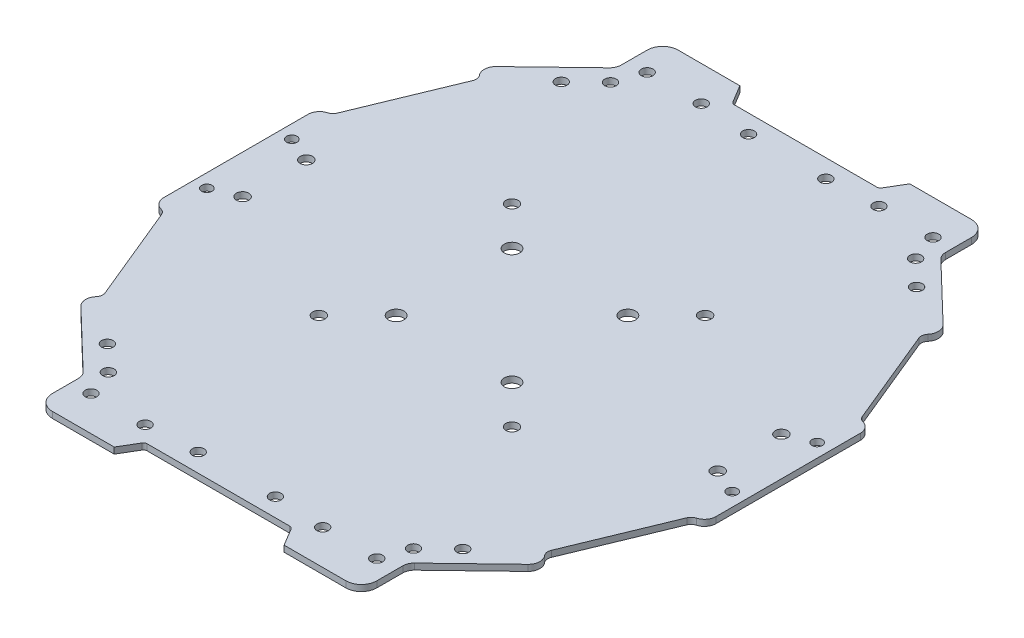
SolidWorks part; units mm, degrees
ref_plane "Front Plane" through (0, 0, 0) normal (0, 0, 1) x (1, 0, 0)
ref_plane "Top Plane" through (0, 0, 0) normal (0, 1, 0) x (1, 0, 0)
ref_plane "Right Plane" through (0, 0, 0) normal (1, 0, 0) x (0, 0, -1)
ref_plane "Plane1"
sketch "Sketch1" plane through (0, 0, 0) normal (0, 1, 0) x (-1, 0, 0)
  line L0 (59.7752, 259.0599) -> (56.7752, 264.0599)
  line L1 (56.7752, 264.0599) -> (36.7752, 264.0599)
  line L2 (36.7752, 264.0599) -> (36.7752, 252.0599)
  line L3 (36.7752, 252.0599) -> (18.7553, 234.7311)
  line L4 (18.7553, 234.7311) -> (21.5279, 231.8479)
  line L5 (21.5279, 231.8479) -> (10.2752, 204.5599)
  line L6 (10.2752, 204.5599) -> (7.2752, 204.5599)
  line L7 (7.2752, 204.5599) -> (7.2752, 183.0599)
  line L8 (7.2752, 183.0599) -> (7.2752, 161.5599)
  line L9 (7.2752, 161.5599) -> (10.2752, 161.5599)
  line L10 (10.2752, 161.5599) -> (21.5279, 134.2718)
  line L11 (21.5279, 134.2718) -> (18.7553, 131.3886)
  line L12 (18.7553, 131.3886) -> (36.7752, 114.0599)
  line L13 (36.7752, 114.0599) -> (36.7752, 102.0599)
  line L14 (36.7752, 102.0599) -> (56.7752, 102.0599)
  line L15 (56.7752, 102.0599) -> (59.7752, 107.0599)
  line L16 (59.7752, 107.0599) -> (78.7752, 107.0599)
  line L17 (78.7752, 107.0599) -> (97.7752, 107.0599)
  line L18 (97.7752, 107.0599) -> (100.7752, 102.0599)
  line L19 (100.7752, 102.0599) -> (120.7752, 102.0599)
  line L20 (120.7752, 102.0599) -> (120.7752, 114.0599)
  line L21 (120.7752, 114.0599) -> (138.795, 131.3886)
  line L22 (138.795, 131.3886) -> (136.0224, 134.2718)
  line L23 (136.0224, 134.2718) -> (147.2752, 161.5599)
  line L24 (147.2752, 161.5599) -> (150.2752, 161.5599)
  line L25 (150.2752, 161.5599) -> (150.2752, 183.0599)
  line L26 (150.2752, 183.0599) -> (150.2752, 204.5599)
  line L27 (150.2752, 204.5599) -> (147.2752, 204.5599)
  line L28 (147.2752, 204.5599) -> (136.0224, 231.8479)
  line L29 (136.0224, 231.8479) -> (138.795, 234.7311)
  line L30 (138.795, 234.7311) -> (120.7752, 252.0599)
  line L31 (120.7752, 252.0599) -> (120.7752, 264.0599)
  line L32 (120.7752, 264.0599) -> (100.7752, 264.0599)
  line L33 (100.7752, 264.0599) -> (97.7752, 259.0599)
  line L34 (97.7752, 259.0599) -> (78.7752, 259.0599)
  line L35 (78.7752, 259.0599) -> (59.7752, 259.0599)
  line L38 (78.7752, 259.0599) -> (78.7752, 107.0599) construction
  line L39 (150.2752, 183.0599) -> (7.2752, 183.0599) construction
  line L85 (91.8838, 199.6325) -> (91.9874, 199.5289)
  line L87 (95.3777, 196.1387) -> (95.4193, 196.097)
  circle A0 centre (55.7752, 111.0599) radius 1.5
  circle A1 centre (39.2752, 118.0599) radius 1.5
  circle A2 centre (53.7752, 208.0599) radius 1.6
  circle A3 centre (53.7752, 158.0599) radius 1.6
  circle A4 centre (17.2752, 174.8099) radius 1.6
  circle A5 centre (103.7752, 158.0599) radius 1.6
  circle A6 centre (93.7752, 198.0599) radius 2
  circle A7 centre (63.7752, 198.0599) radius 2
  circle A8 centre (63.7752, 168.0599) radius 2
  circle A9 centre (93.7752, 168.0599) radius 2
  circle A22 centre (41.7752, 255.0599) radius 1.5
  circle A23 centre (39.2752, 248.0599) radius 1.5
  circle A24 centre (10.7752, 194.0599) radius 1.35
  circle A25 centre (88.7752, 111.8099) radius 1.5
  circle A27 centre (115.7752, 111.0599) radius 1.5
  circle A28 centre (118.2752, 118.0599) radius 1.5
  circle A29 centre (140.2752, 174.8099) radius 1.6
  circle A30 centre (115.7752, 255.0599) radius 1.5
  circle A31 centre (88.7752, 254.3099) radius 1.5
  circle A32 centre (140.2752, 191.3099) radius 1.6
  circle A33 centre (146.7752, 194.0599) radius 1.35
  circle A53 centre (101.7752, 255.0599) radius 1.5
  circle A54 centre (118.2752, 248.0599) radius 1.5
  circle A55 centre (146.7752, 172.0599) radius 1.35
  circle A57 centre (101.7752, 111.0599) radius 1.5
  circle A69 centre (17.2752, 191.3099) radius 1.6
  circle A71 centre (55.7752, 255.0599) radius 1.5
  circle A73 centre (68.7752, 254.3099) radius 1.5
  circle A74 centre (10.7752, 172.0599) radius 1.35
  circle A76 centre (68.7752, 111.8099) radius 1.5
  circle A77 centre (41.7752, 111.0599) radius 1.5
  circle A82 centre (32.7752, 124.3099) radius 1.5
  circle A86 centre (124.7752, 241.8099) radius 1.5
  circle A87 centre (32.7752, 241.8099) radius 1.5
  circle A90 centre (103.7752, 208.0599) radius 1.6
  circle A91 centre (124.7752, 124.3099) radius 1.5
  point P41 (150.2752, 193.8099)
  point P57 (0, 0)
  dimension "D1" = 143
  dimension "D2" = 162
  dimension "D5" = 15
  dimension "D3" = 25
  dimension "D4" = 25
  dimension "D6" = 15
extrude "Extrusion1" add sketch "Sketch1" along normal blind 1.6
fillet "Fillet1" radius 1 4 edges at (-97.7752, 0.8, 107.0599) (-59.7752, 0.8, 107.0599) (-59.7752, 0.8, 259.0599) (-97.7752, 0.8, 259.0599)
fillet "Fillet2" radius 4 4 edges at (-120.7752, 0.8, 102.0599) (-36.7752, 0.8, 102.0599) (-120.7752, 0.8, 264.0599) (-36.7752, 0.8, 264.0599)
fillet "Fillet3" radius 3 4 edges at (-120.7752, 0.8, 114.0599) (-36.7752, 0.8, 114.0599) (-36.7752, 0.8, 252.0599) (-120.7752, 0.8, 252.0599)
fillet "Fillet4" radius 3 1 edges at (-138.795, 0.8, 234.7311)
fillet "Fillet5" radius 2 1 edges at (-136.0224, 0.8, 231.8479)
fillet "Fillet6" radius 2 1 edges at (-21.5279, 0.8, 231.8479)
fillet "Fillet7" radius 3 1 edges at (-18.7553, 0.8, 234.7311)
fillet "Fillet8" radius 3 2 edges at (-138.795, 0.8, 131.3886) (-18.7553, 0.8, 131.3886)
fillet "Fillet9" radius 2 2 edges at (-21.5279, 0.8, 134.2718) (-136.0224, 0.8, 134.2718)
fillet "Fillet10" radius 2 4 edges at (-10.2752, 0.8, 161.5599) (-10.2752, 0.8, 204.5599) (-147.2752, 0.8, 204.5599) (-147.2752, 0.8, 161.5599)
fillet "Fillet11" radius 3 4 edges at (-150.2752, 0.8, 161.5599) (-150.2752, 0.8, 204.5599) (-7.2752, 0.8, 204.5599) (-7.2752, 0.8, 161.5599)
